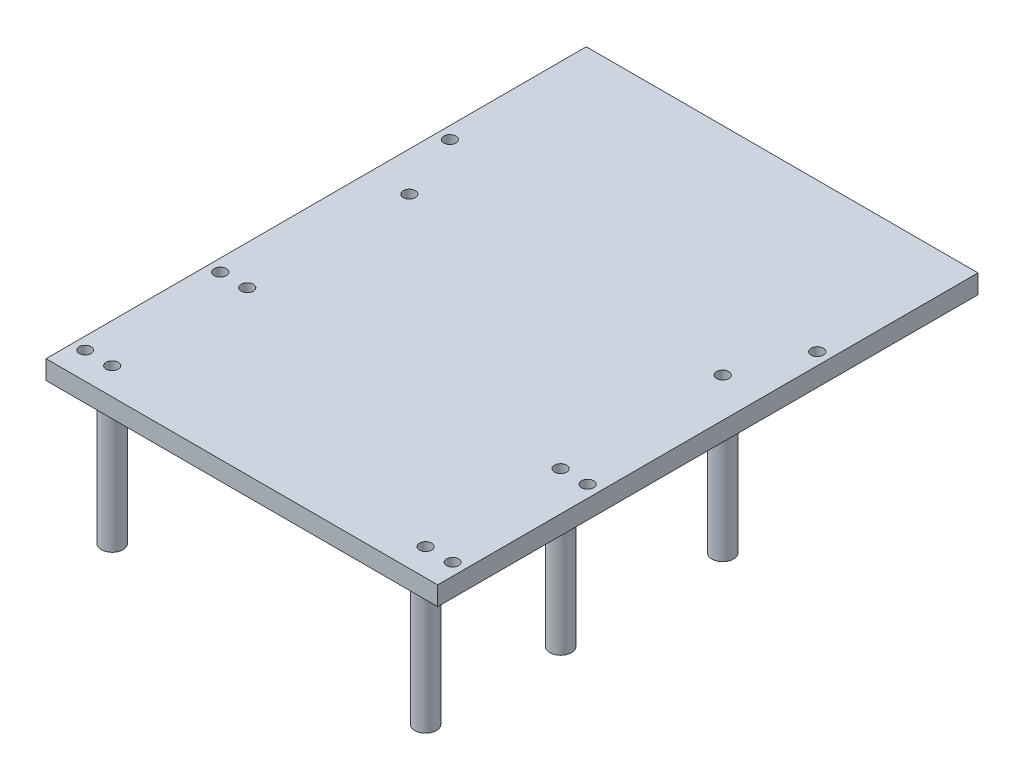
SolidWorks part; units mm, degrees
ref_plane "Front Plane" through (0, 0, 0) normal (0, 0, 1) x (1, 0, 0)
ref_plane "Top Plane" through (0, 0, 0) normal (0, 1, 0) x (1, 0, 0)
ref_plane "Right Plane" through (0, 0, 0) normal (1, 0, 0) x (0, 0, -1)
sketch "Sketch2" plane through (0, 0, 0) normal (0, 1, 0) x (1, 0, 0)
  line L1 (72.5, -100) -> (-72.5, -100)
  line L2 (72.5, -100) -> (72.5, 100)
  line L3 (72.5, 100) -> (-72.5, 100)
  line L4 (-72.5, -100) -> (-72.5, 100)
  line L5 (72.5, -100) -> (-72.5, 100) construction
  line L6 (72.5, 100) -> (-72.5, -100) construction
  point P0 (0, 0)
  dimension "D1" = 200
  dimension "D2" = 145
extrude "Boss-Extrude1" add sketch "Sketch2" along normal blind 7
sketch "Sketch3" plane through (0, 7, 0) normal (0, 1, 0) x (1, 0, 0)
  line L0 (-72.5, -100) -> (72.5, -100) construction
  line L1 (-72.5, 100) -> (-72.5, -100) construction
  line L2 (0, -116.5461) -> (0, 123.1136) construction
  circle A0 centre (-68, -90) radius 4
  circle A1 centre (-68, -40) radius 4
  circle A2 centre (-68, 45) radius 4
  circle A5 centre (68, 45) radius 4
  circle A6 centre (68, -40) radius 4
  circle A7 centre (68, -90) radius 4
  dimension "D1" = 8
  dimension "D2" = 8
  dimension "D6" = 8
  dimension "D3" = 10
  dimension "D4" = 4.5
  dimension "D5" = 50
  dimension "D7" = 85
sketch "Sketch5" plane through (0, 32, 0) normal (0, 1, 0) x (1, 0, 0)
  line L0 (0, 117.1982) -> (0, -112.4984) construction
  circle A0 centre (-68, 45) radius 2.25
  circle A1 centre (-68, -40) radius 2.25
  circle A2 centre (-68, -90) radius 2.2
  circle A3 centre (68, -90) radius 2.2
  circle A4 centre (68, -40) radius 2.25
  circle A5 centre (68, 45) radius 2.25
  dimension "D1" = 4.5
  dimension "D2" = 4.5
  dimension "D3" = 4.4
extrude "Cut-Extrude1" cut sketch "Sketch5" against normal through all
sketch "Sketch6" plane through (0, 0, 0) normal (0, -1, 0) x (1, 0, 0)
  line L0 (0, 114.2827) -> (0, -38.7376) construction
  line L1 (58, -20) -> (-58, -20)
  line L2 (58, -20) -> (58, 90)
  line L3 (58, 90) -> (-58, 90)
  line L4 (-58, -20) -> (-58, 90)
  line L5 (58, -20) -> (-58, 90) construction
  line L6 (58, 90) -> (-58, -20) construction
  circle A0 centre (68, 40) radius 2.25 construction
  circle A1 centre (-68, 40) radius 2.25 construction
  circle A2 centre (68, 90) radius 2.2 construction
  circle A3 centre (-68, 90) radius 2.2 construction
  circle A4 centre (68, 40) radius 2.25
  circle A5 centre (-68, 40) radius 2.25
  circle A6 centre (68, 90) radius 2.2
  circle A7 centre (-68, 90) radius 2.2
  circle A8 centre (-58, 90) radius 4
  circle A9 centre (-58, 40) radius 4
  circle A10 centre (-58, -20) radius 4
  circle A11 centre (58, -20) radius 4
  circle A12 centre (58, 40) radius 4
  circle A13 centre (58, 90) radius 4
  point P0 (0, 35)
  dimension "D4" = 8
  dimension "D1" = 10
  dimension "D2" = 10
  dimension "D3" = 110
extrude "Boss-Extrude3" add sketch "Sketch6" along normal blind 50 contours L4 A9 | L4 A9 | L3 A8 L4 | L4 A8 L3 | A13 | A10 | A11 | A12
sketch "Sketch7" plane through (0, -50, 0) normal (0, -1, 0) x (1, 0, 0)
  line L0 (0, 107.399) -> (0, -110.0377) construction
  circle A0 centre (-58, 90) radius 2.25
  circle A2 centre (-58, 40) radius 2.25
  circle A3 centre (-58, -20) radius 2.25
  circle A4 centre (58, -20) radius 2.25
  circle A5 centre (58, 40) radius 2.25
  circle A6 centre (58, 90) radius 2.25
  dimension "D1" = 4.5
extrude "Cut-Extrude2" cut sketch "Sketch7" against normal through all
